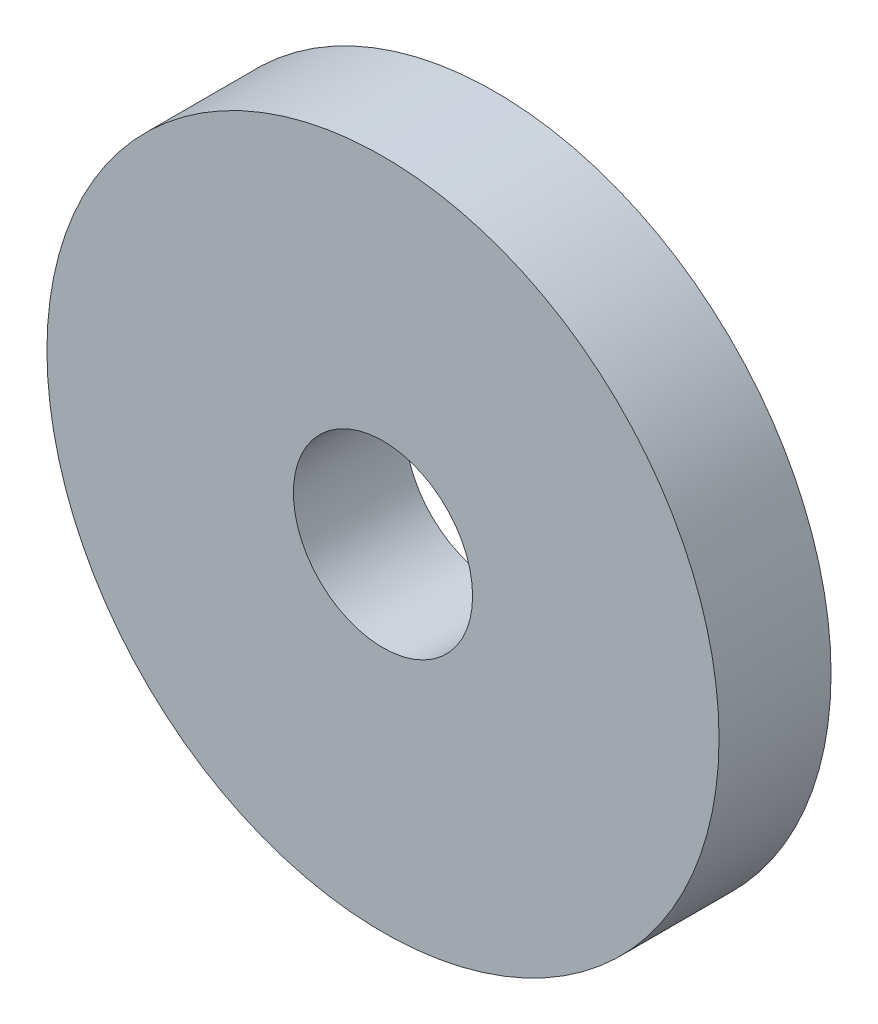
SolidWorks part; units mm, degrees
ref_plane "Alzado" through (0, 0, 0) normal (0, 0, 1) x (1, 0, 0)
ref_plane "Planta" through (0, 0, 0) normal (0, 1, 0) x (1, 0, 0)
ref_plane "Vista lateral" through (0, 0, 0) normal (1, 0, 0) x (0, 0, -1)
sketch "Croquis1" plane through (0, 0, 0) normal (0, 0, 1) x (1, 0, 0)
  circle A0 centre (0, 0) radius 1.6
  circle A1 centre (0, 0) radius 6
extrude "Arandela espaciadora" add sketch "Croquis1" along normal blind 2
